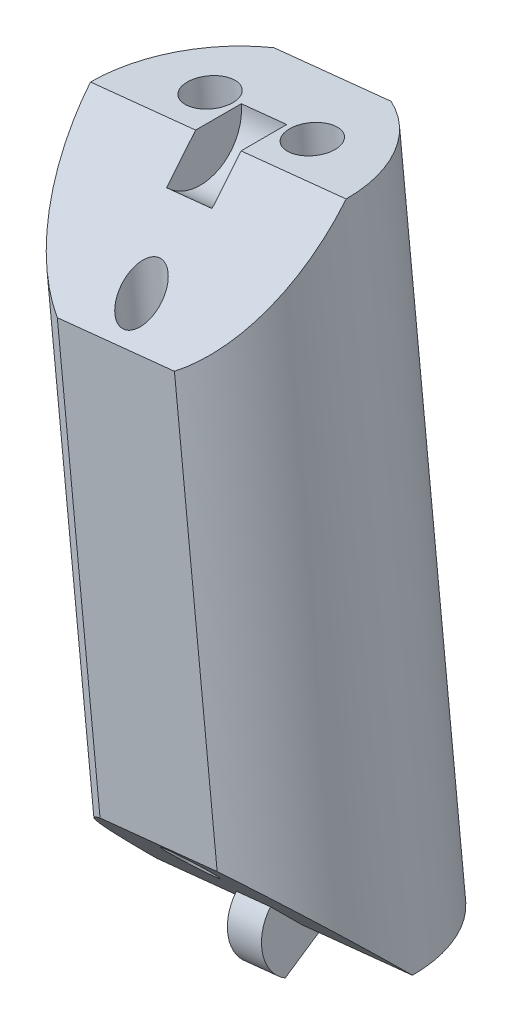
SolidWorks part; units mm, degrees
ref_plane "Front Plane" through (0, 0, 0) normal (0, 0, 1) x (1, 0, 0)
ref_plane "Top Plane" through (0, 0, 0) normal (0, 1, 0) x (1, 0, 0)
ref_plane "Right Plane" through (0, 0, 0) normal (1, 0, 0) x (0, 0, -1)
sketch "Sketch2" plane through (0, 0, 0) normal (0, 0, 1) x (1, 0, 0)
  line L0 (0, 0) -> (90, 0)
  line L1 (90, 0) -> (90, 120)
  line L2 (90, 120) -> (0, 120)
  line L3 (0, 120) -> (0, 0)
  line L4 (0, 120) -> (-10, 120)
  line L5 (-10, 120) -> (-10, 16.9491)
  line L6 (-10, 120) -> (57.5, 127)
  line L7 (57.5, 127) -> (90, 124)
  line L8 (90, 120) -> (99, 60)
  line L10 (90, 124) -> (90, 120)
  line L11 (5.9147, 0) -> (5.9147, -25)
  line L12 (5.9147, -25) -> (-4.0853, -25)
  line L13 (-4.0853, -29) -> (-4.0853, 0)
  line L14 (80, 0) -> (80, -25)
  line L15 (80, -25) -> (90, -25)
  line L16 (90, -29) -> (90, 0)
  line L17 (15.7927, 122.6748) -> (5.4776, 222.1414)
  line L18 (5.4776, 222.1414) -> (21.3923, 223.7918)
  line L19 (21.3923, 223.7918) -> (31.7073, 124.3252)
  line L20 (7.6492, 201.201) -> (23.5639, 202.8514)
  line L21 (10.9066, 169.7905) -> (26.8212, 171.441)
  line L22 (-10, 120) -> (-20.0396, 216.8108)
  line L23 (-20.0396, 216.8108) -> (-4.125, 218.4612)
  line L24 (-4.125, 218.4612) -> (5.9147, 121.6504)
  line L25 (-17.926, 196.4296) -> (-2.0114, 198.08)
  line L26 (-14.7556, 165.8578) -> (1.159, 167.5082)
  line L27 (57.5, 127) -> (46.9095, 229.1223)
  line L28 (46.9095, 229.1223) -> (30.9949, 227.4719)
  line L29 (30.9949, 227.4719) -> (41.5853, 125.3496)
  line L30 (33.2245, 205.9725) -> (49.1391, 207.6229)
  line L31 (36.5688, 173.7233) -> (52.4835, 175.3737)
  line L34 (90, 124) -> (99.1917, 223.5767)
  line L35 (99.1917, 223.5767) -> (83.2594, 225.0473)
  line L36 (83.2594, 225.0473) -> (74.0677, 125.4707)
  line L38 (81.3243, 204.0838) -> (97.2566, 202.6132)
  line L39 (78.4217, 172.6386) -> (94.354, 171.1679)
  line L40 (62.4078, 79.6749) -> (57.5, 127) construction
  line L41 (41.5853, 125.3496) -> (46.4931, 78.0244) construction
  line L42 (46.4931, 78.0244) -> (62.4078, 79.6749) construction
  line L43 (31.7073, 124.3252) -> (36.6151, 77.0001) construction
  line L44 (36.6151, 77.0001) -> (20.7005, 75.3496) construction
  line L45 (20.7005, 75.3496) -> (15.7927, 122.6748) construction
  line L46 (5.9147, 121.6504) -> (10.8224, 74.3253) construction
  line L47 (10.8224, 74.3253) -> (-5.0922, 72.6749) construction
  line L48 (-5.0922, 72.6749) -> (-10, 120) construction
  line L49 (74.0677, 125.4707) -> (69.6944, 78.0931) construction
  line L50 (69.6944, 78.0931) -> (85.7624, 78.0931) construction
  line L51 (85.7624, 78.0931) -> (90, 124) construction
  line L52 (-12.0823, 217.636) -> (10.4873, 0) construction
  line L53 (13.4349, 222.9666) -> (36.5574, 0) construction
  line L54 (38.9522, 228.2971) -> (62.6275, 0) construction
  line L55 (91.2256, 224.312) -> (70.5198, 0) construction
  line L59 (99, 60) -> (93.5277, 44.9649)
  line L60 (99, 60) -> (169.4769, 34.3485)
  line L61 (169.4769, 34.3485) -> (164.0046, 19.3134)
  line L62 (164.0046, 19.3134) -> (93.5277, 44.9649)
  line L63 (90, -2) -> (100, -2)
  line L64 (141.2862, 44.6091) -> (135.8138, 29.574)
  line L65 (99, 60) -> (55.7741, 75.7329) construction
  line L66 (55.7741, 75.7329) -> (50.3018, 60.6978) construction
  line L67 (100, -2) -> (100, -29)
  line L70 (-4.0853, -2) -> (-14.0853, -2)
  line L71 (-14.0853, -2) -> (-14.0853, -29)
  line L74 (-4.0853, 0) -> (0, 0)
  line L75 (-14.0853, -29) -> (-14.0853, -112.587)
  line L76 (-14.0853, -112.587) -> (100, -112.587)
  line L77 (100, -112.587) -> (100, -29)
  line L78 (-14.0853, -29) -> (100, -29)
  line L79 (-14.0853, -14.5) -> (100, -14.5) construction
  line L80 (31.7073, -112.587) -> (31.7073, -122.6232)
  line L81 (31.7073, -122.6232) -> (42.9573, -122.6232)
  line L82 (42.9573, -122.6232) -> (42.9573, -112.587)
  line L83 (-14.0853, -112.587) -> (-88.3667, -112.587)
  line L84 (-88.3667, -112.587) -> (-88.3667, -128.2699)
  line L85 (-88.3667, -128.2699) -> (169.4958, -128.2699)
  line L86 (169.4958, -128.2699) -> (169.4958, -112.587)
  line L87 (169.4958, -112.587) -> (100, -112.587)
  line L88 (90, 60) -> (-10, 60) construction
  line L89 (50.3018, 60.6978) -> (93.5277, 44.9649) construction
  line L90 (87.2806, 55.7521) -> (166.7408, 26.8309) construction
  line L91 (87.2806, 55.7521) -> (82.1749, 52.5336) construction
  line L92 (82.1749, 52.5336) -> (77.3257, 0) construction
  line L93 (83.1185, 56.6957) -> (86.337, 51.59) construction
  arc A0 (-10, 16.9491) -> (-4.0853, 0) centre (14.9876, 16.1624) ccw
  arc A1 (93.5277, 44.9649) -> (90, 0) centre (-126.4069, 39.5988) cw
  point P42 (41.1818, 206.7977)
  point P100 (84.7278, 54.1428)
  point P101 (84.7278, 54.1428)
  dimension "D11" = 47.3684
  dimension "D35" = 9
  dimension "D32" = 220
  dimension "D36" = 25
  dimension "D1" = 120
  dimension "D2" = 90
  dimension "D3" = 10
  dimension "D5" = 67.862
  dimension "D6" = 7
  dimension "D7" = 4
  dimension "D8" = 16
  dimension "D9" = 16
  dimension "D10" = 100
  dimension "D12" = 31.5789
  dimension "D13" = 16
  dimension "D14" = 16
  dimension "D15" = 16
  dimension "D16" = 25.7927
  dimension "D17" = 100
  dimension "D18" = 21.0526
  dimension "D19" = 31.5789
  dimension "D20" = 97.33
  dimension "D21" = 102.67
  dimension "D22" = 20.4905
  dimension "D23" = 30.7358
  dimension "D24" = 21.6147
  dimension "D25" = 32.4221
  dimension "D26" = 25
  dimension "D28" = 25
  dimension "D29" = 75
  dimension "D30" = 47.5789
  dimension "D31" = 30
  dimension "D33" = 46
  dimension "D34" = 20
  dimension "D37" = 2
  dimension "D38" = 2
  dimension "D39" = 27
  dimension "D40" = 10
  dimension "D41" = 10
  dimension "D42" = 27
  dimension "D43" = 14.5
  dimension "D44" = 127.5
ref_plane "Plane1" through (87.2806, 55.7521, 0) normal (-0.846, -0.5333, 0) x (0, 0, 1)
ref_plane "Plane2" through (82.1749, 52.5336, 0) normal (-0.0919, -0.9958, 0) x (-0.9958, 0.0919, 0)
ref_plane "Plane3" through (91.2256, 224.312, 0) normal (-0.0919, -0.9958, 0) x (-0.9958, 0.0919, 0)
ref_plane "Plane4" through (38.9522, 228.2971, 0) normal (0.1032, -0.9947, 0) x (-0.9947, -0.1032, 0)
ref_plane "Plane5" through (13.4349, 222.9666, 0) normal (0.1032, -0.9947, 0) x (-0.9947, -0.1032, 0)
ref_plane "Plane7" through (166.7408, 26.8309, 0) normal (0.9397, -0.342, 0) x (0, 0, -1)
ref_plane "Plane8" through (110.4217, -40.1902, 0) normal (0.9397, -0.342, 0) x (0, 0, -1)
ref_plane "Plane9" through (19.3664, 209.803, 0) normal (-0.0919, -0.9958, 0) x (-0.9958, 0.0919, 0)
ref_plane "Plane10" through (16.4638, 178.3578, 0) normal (-0.0919, -0.9958, 0) x (-0.9958, 0.0919, 0)
ref_plane "Plane11" through (-20.7793, 200.3721, 0) normal (0.1032, -0.9947, 0) x (-0.9947, -0.1032, 0)
ref_plane "Plane12" through (-17.435, 168.1229, 0) normal (0.1032, -0.9947, 0) x (-0.9947, -0.1032, 0)
ref_plane "Plane13" through (-20.5619, 198.2754, 0) normal (0.1032, -0.9947, 0) x (-0.9947, -0.1032, 0)
ref_plane "Plane14" through (-17.3045, 166.8649, 0) normal (0.1032, -0.9947, 0) x (-0.9947, -0.1032, 0)
ref_plane "Plane15" through (-12.0823, 217.636, 0) normal (0.1032, -0.9947, 0) x (-0.9947, -0.1032, 0)
ref_plane "Plane16" through (-20.3445, 196.1788, 0) normal (0.1032, -0.9947, 0) x (-0.9947, -0.1032, 0)
ref_plane "Plane17" through (-17.1741, 165.607, 0) normal (0.1032, -0.9947, 0) x (-0.9947, -0.1032, 0)
ref_plane "Plane18" through (12.1098, 131.1899, 0) normal (-0.0919, -0.9958, 0) x (-0.9958, 0.0919, 0)
ref_plane "Plane19" through (-12.4184, 119.7492, 0) normal (0.1032, -0.9947, 0) x (-0.9947, -0.1032, 0)
ref_plane "Plane20" through (0, 0, 0) normal (0, 0, 1) x (0.1032, -0.9947, 0)
ref_plane "Plane21" through (0, 0, 0) normal (0, 0, 1) x (-0.0919, -0.9958, 0)
ref_plane "Plane22" through (10.3758, 1.076, 0) normal (-0.9947, -0.1032, 0) x (0.1032, -0.9947, 0)
ref_plane "Plane23" through (36.1684, 3.7508, 0) normal (-0.9947, -0.1032, 0) x (0.1032, -0.9947, 0)
ref_plane "Plane24" through (61.9611, 6.4256, 0) normal (-0.9947, -0.1032, 0) x (0.1032, -0.9947, 0)
ref_plane "Plane25" through (69.924, -6.4545, 0) normal (-0.9958, 0.0919, 0) x (-0.0919, -0.9958, 0)
sketch "Sketch3" plane through (-20.3445, 196.1788, 0) normal (0.1032, -0.9947, 0) x (-0.9947, -0.1032, 0)
  line L0 (-2.4314, 0) -> (-18.4314, 0) construction
  circle A0 centre (-10.4314, 0) radius 9
  dimension "D1" = 18
extrude "Boss-Extrude1" add sketch "Sketch3" along normal blind 45
sketch "Sketch4" plane through (10.3758, 1.076, 0) normal (-0.9947, -0.1032, 0) x (0.1032, -0.9947, 0)
  line L0 (-197.2309, 0) -> (-188.2309, 9)
  line L1 (-197.2309, 9) -> (-197.2309, -9) construction
  line L2 (-152.2309, 9) -> (-197.2309, 9) construction
  line L3 (-188.2309, 9) -> (-197.2309, 9)
  line L4 (-197.2309, 9) -> (-197.2309, 0)
  line L5 (-161.2309, 9) -> (-152.2309, 9)
  line L6 (-152.2309, 9) -> (-152.2309, 0)
  line L7 (-217.7214, 0) -> (1.0818, 0) construction
  line L8 (-152.2309, 0) -> (-161.2309, 9)
  dimension "D1" = 45
  dimension "D2" = 45
extrude "Cut-Extrude1" cut sketch "Sketch4" against normal through all and the other way through all
sketch "Sketch5" plane through (10.3758, 1.076, 0) normal (-0.9947, -0.1032, 0) x (0.1032, -0.9947, 0)
  line L0 (-152.2309, 0) -> (-154.2108, 1.9799)
  line L1 (-152.2309, 0) -> (-161.2309, 9) construction
  line L6 (-152.2309, -2.8) -> (-149.806, 1.4)
  line L8 (-152.2309, -9) -> (-152.2309, 0) construction
  line L10 (-152.2309, 0) -> (-152.2309, -2.8)
  arc A0 (-154.2108, 1.9799) -> (-149.806, 1.4) centre (-152.2309, 0) cw
  dimension "D1" = 2.8
  dimension "D2" = 30
extrude "Boss-Extrude2" add sketch "Sketch5" along normal mid plane 2.4
sketch "Sketch7" plane through (10.3758, 1.076, 0) normal (-0.9947, -0.1032, 0) x (0.1032, -0.9947, 0)
  line L6 (-217.7214, 0) -> (1.0818, 0) construction
  line L7 (-194.9681, 2.2627) -> (-197.2309, 0)
  line L8 (-197.2309, 0) -> (-197.2309, -3.2)
  line L9 (-188.2309, 9) -> (-197.2309, 0) construction
  arc A1 (-197.2309, -3.2) -> (-194.9681, 2.2627) centre (-197.2309, 0) ccw
  dimension "D1" = 3.2
extrude "Cut-Extrude2" cut sketch "Sketch7" against normal mid plane 3.2
sketch "Sketch8" plane through (-20.3445, 196.1788, 0) normal (-0.1032, 0.9947, 0) x (0.9947, 0.1032, 0)
  line L0 (2.4314, 0) -> (18.4314, 0) construction
  circle A0 centre (6.8314, 3) radius 1.6
  circle A1 centre (14.0314, 3) radius 1.6
  circle A2 centre (10.4314, -6) radius 1.4
  point P9 (10.4314, 0)
  dimension "D1" = 3.2
  dimension "D2" = 3.2
  dimension "D3" = 2.8
  dimension "D4" = 3
  dimension "D5" = 3
  dimension "D6" = 3.6
  dimension "D7" = 3.6
  dimension "D8" = 6
extrude "Cut-Extrude3" cut sketch "Sketch8" against normal through all and the other way through all
sketch "Sketch9" plane through (-15.7027, 151.4188, 0) normal (0.1032, -0.9947, 0) x (0.9947, 0.1032, 0)
  line L0 (6.3083, -8) -> (14.5545, -8)
  line L1 (14.5545, 8) -> (6.3083, 8)
  line L2 (2.4314, 0) -> (18.4314, 0) construction
  line L3 (2.4314, 0) -> (70.2934, 0) construction
  arc A0 (1.4314, 0) -> (19.4314, 0) centre (10.4314, 0) ccw construction
  arc A1 (6.3083, -8) -> (14.5545, -8) centre (10.4314, 0) ccw
  arc A3 (19.4314, 0) -> (1.4314, 0) centre (10.4314, 0) ccw construction
  arc A4 (6.3083, 8) -> (14.5545, 8) centre (10.4314, 0) cw
  dimension "D1" = 8
  dimension "D2" = 8
extrude "Cut-Extrude4" cut sketch "Sketch9" against normal through all
